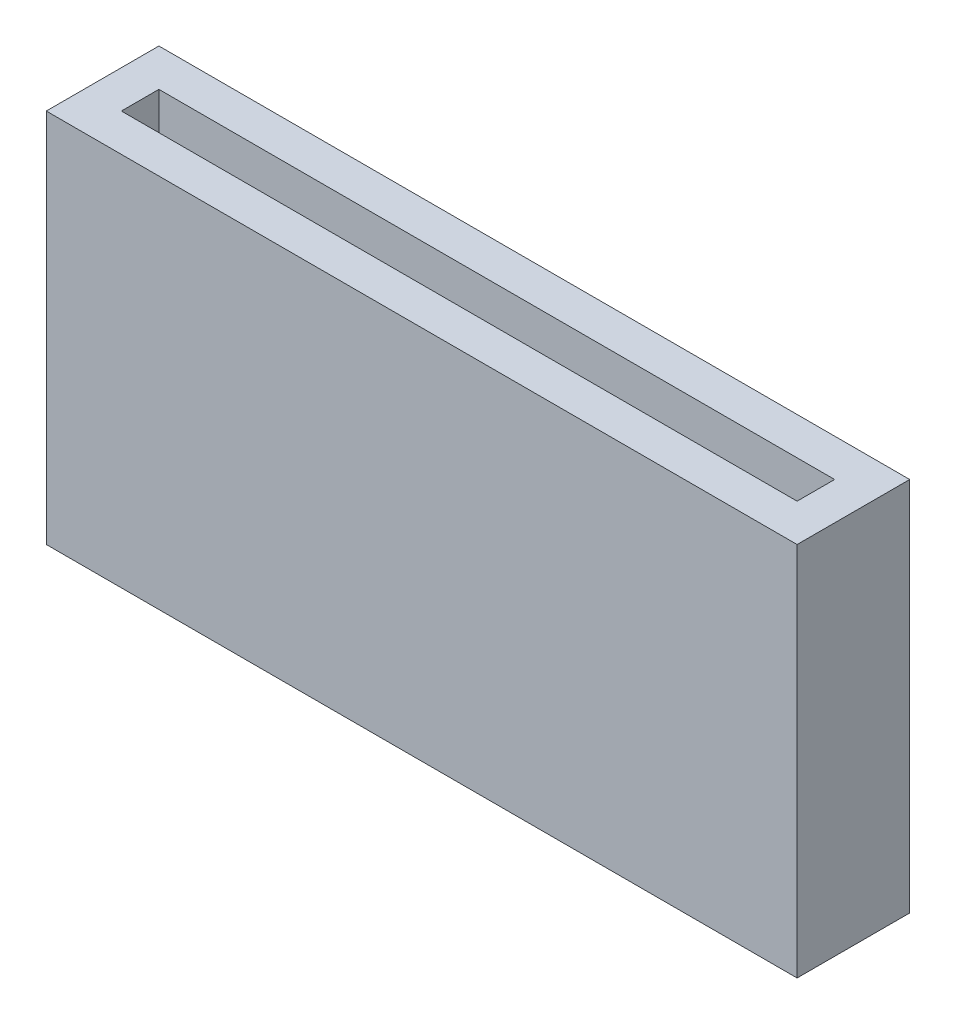
SolidWorks part; units mm, degrees
ref_plane "Front Plane" through (0, 0, 0) normal (0, 0, 1) x (1, 0, 0)
ref_plane "Top Plane" through (0, 0, 0) normal (0, 1, 0) x (1, 0, 0)
ref_plane "Right Plane" through (0, 0, 0) normal (1, 0, 0) x (0, 0, -1)
sketch "Sketch2" plane through (0, 0, 0) normal (0, 0, 1) x (1, 0, 0)
  line L1 (-4, 2) -> (4, 2)
  line L2 (-4, 2) -> (-4, -2)
  line L3 (-4, -2) -> (4, -2)
  line L4 (4, 2) -> (4, -2)
  line L5 (-4, 2) -> (4, -2) construction
  line L6 (-4, -2) -> (4, 2) construction
  point P0 (0, 0)
  dimension "D1" = 8
  dimension "D2" = 4
extrude "Boss-Extrude1" add sketch "Sketch2" along normal blind 0.4
sketch "Sketch3" plane through (0, 0, 0.4) normal (0, 0, 1) x (1, 0, 0)
  line L0 (-4, -2) -> (4, -2) construction
  line L1 (-4, 2) -> (-3.6, 2)
  line L2 (-4, 2) -> (-4, -2)
  line L3 (-4, -2) -> (-3.6, -2)
  line L4 (-3.6, 2) -> (-3.6, -2)
  dimension "D1" = 0.4
extrude "Boss-Extrude2" add sketch "Sketch3" along normal blind 0.8
sketch "Sketch4" plane through (0, 0, 0.4) normal (0, 0, 1) x (1, 0, 0)
  line L0 (-3.6, -2) -> (4, -2) construction
  line L1 (4, 2) -> (3.6, 2)
  line L2 (4, 2) -> (4, -2)
  line L3 (4, -2) -> (3.6, -2)
  line L4 (3.6, 2) -> (3.6, -2)
  dimension "D1" = 0.4
extrude "Boss-Extrude3" add sketch "Sketch4" along normal blind 0.8
sketch "Sketch5" plane through (-3.6, 0, 0) normal (1, 0, 0) x (0, 0, -1)
  line L0 (-1.2, -2) -> (-0.4, -2) construction
  line L1 (-1.2, 2) -> (-0.8, 2)
  line L2 (-1.2, 2) -> (-1.2, -2)
  line L3 (-1.2, -2) -> (-0.8, -2)
  line L4 (-0.8, 2) -> (-0.8, -2)
  dimension "D1" = 0.4
extrude "Boss-Extrude4" add sketch "Sketch5" along normal up to next
